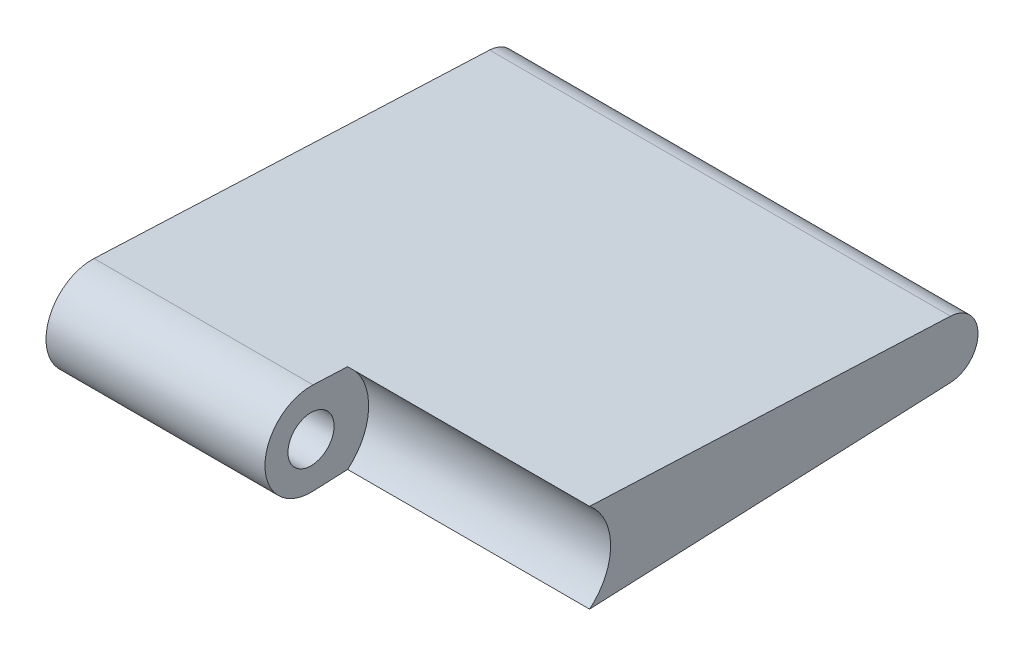
SolidWorks part; units mm, degrees
material "AISI 1035 Steel (SS)"
ref_plane "Front Plane" through (0, 0, 0) normal (0, 0, 1) x (1, 0, 0)
ref_plane "Top Plane" through (0, 0, 0) normal (0, 1, 0) x (1, 0, 0)
ref_plane "Right Plane" through (0, 0, 0) normal (1, 0, 0) x (0, 0, -1)
sketch "Sketch1" plane through (0, 0, 0) normal (1, 0, 0) x (0, 0, -1)
  line L0 (-6.3469, -1.5657) -> (7.1099, -0.9795)
  line L1 (-6.3469, 1.5657) -> (7.1099, 0.9795)
  arc A0 (-6.3469, 1.5657) -> (-6.3469, -1.5657) centre (-6.4151, 0) ccw
  arc A1 (7.1099, -0.9795) -> (7.1099, 0.9795) centre (7.0672, 0) ccw
  circle A2 centre (-6.4151, 0) radius 0.7849
  dimension "D1" = 13.4823
extrude "Boss-Extrude1" add sketch "Sketch1" against normal blind 15.682
sketch "Sketch2" plane through (0, 0, 0) normal (1, 0, 0) x (0, 0, -1)
  circle A0 centre (-6.4151, 0) radius 1.9609
extrude "Cut-Extrude1" cut sketch "Sketch2" against normal blind 8.2321
